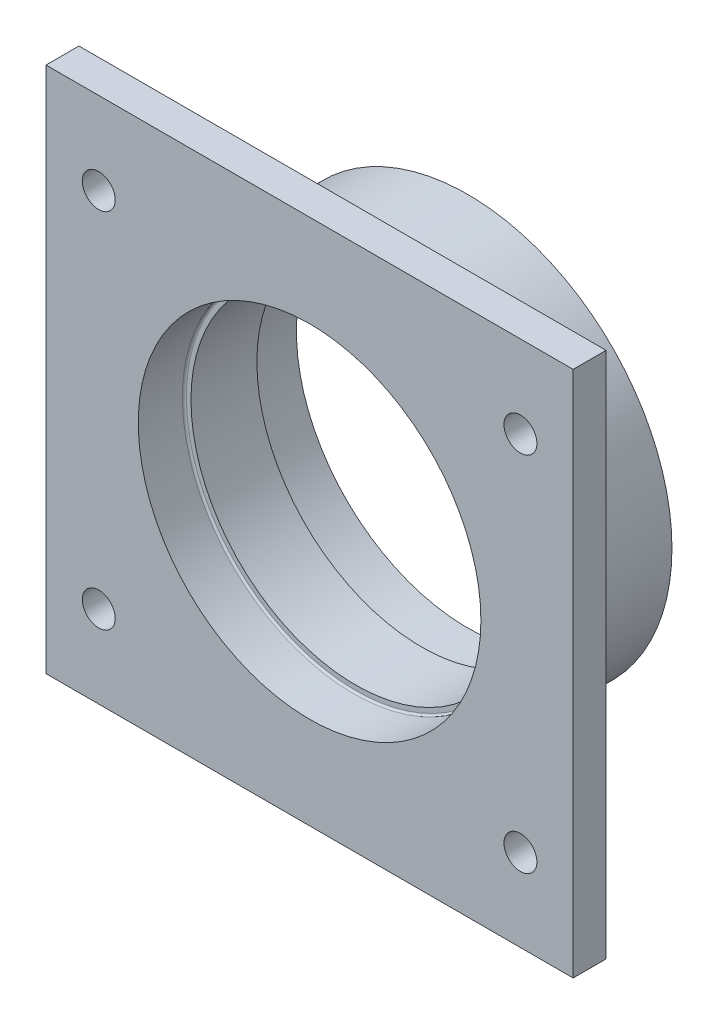
SolidWorks part; units mm, degrees
material "6061 Alloy"
ref_plane "Front Plane" through (0, 0, 0) normal (0, 0, 1) x (1, 0, 0)
ref_plane "Top Plane" through (0, 0, 0) normal (0, 1, 0) x (1, 0, 0)
ref_plane "Right Plane" through (0, 0, 0) normal (1, 0, 0) x (0, 0, -1)
sketch "Sketch1" plane through (0, 0, 0) normal (0, 0, 1) x (1, 0, 0)
  circle A0 centre (0, 0) radius 26
  circle A1 centre (0, 0) radius 31
  dimension "D1" = 52
  dimension "D2" = 5
extrude "Boss-Extrude1" add sketch "Sketch1" along normal blind 7
sketch "Sketch2" plane through (0, 0, 7) normal (0, 0, 1) x (1, 0, 0)
  circle A0 centre (0, 0) radius 31
  circle A1 centre (0, 0) radius 25
  dimension "D1" = 62
  dimension "D2" = 50
extrude "Boss-Extrude3" add sketch "Sketch2" along normal blind 10
sketch "Sketch3" plane through (0, 0, 17) normal (0, 0, 1) x (1, 0, 0)
  circle A0 centre (0, 0) radius 26
  circle A1 centre (0, 0) radius 31
  dimension "D1" = 62
  dimension "D2" = 52
extrude "Boss-Extrude4" add sketch "Sketch3" along normal blind 7
fillet "Fillet1" radius 0.3 2 edges at (26, 0, 7) (26, 0, 17)
sketch "Sketch4" plane through (0, 0, 24) normal (0, 0, 1) x (1, 0, 0)
  line L1 (-40, -40) -> (40, -40)
  line L2 (-40, -40) -> (-40, 40)
  line L3 (-40, 40) -> (40, 40)
  line L4 (40, -40) -> (40, 40)
  line L5 (-40, -40) -> (40, 40) construction
  line L6 (-40, 40) -> (40, -40) construction
  circle A0 centre (0, 0) radius 31
  dimension "D1" = 62
  dimension "D2" = 80
  dimension "D3" = 80
extrude "Boss-Extrude5" add sketch "Sketch4" against normal blind 5
fillet "Fillet2" radius 2 1 edges at (31, 0, 19)
hole_wizard "M6x1.0 Tapped Hole1" positions "Sketch5" profile "Sketch6" tap size "M6x1.0" standard "ANSI Metric" end condition through all
sketch "Sketch5" plane through (0, 0, 24) normal (0, 0, 1) x (1, 0, 0)
  line L0 (40, -40) -> (40, 40) construction
  line L2 (40, 40) -> (-40, 40) construction
  point P0 (-32, 27.5)
  point P2 (32, 27.5)
  point P4 (32, -27.5)
  point P6 (-32, -27.5)
  point P9 (0, 0)
  point P10 (0, 0)
  point P11 (0, 0)
  point P12 (0, 0)
  dimension "D1" = 64
  dimension "D2" = 8
  dimension "D3" = 55
  dimension "D4" = 12.5
sketch "Sketch6" plane through (-32, 27.5, 24) normal (1, 0, 0) x (0, -1, 0)
  line L0 (0, 0) -> (0, 24)
  line L1 (0, 24) -> (2.5, 24)
  line L2 (2.5, 24) -> (2.5, 0)
  line L5 (2.5, 0) -> (0, 0)
  line L11 (0, -6.35) -> (0, 107.95) construction
  dimension "Thread Major Dia." = 5
  dimension "Thru Tap Drill Depth" = 24
